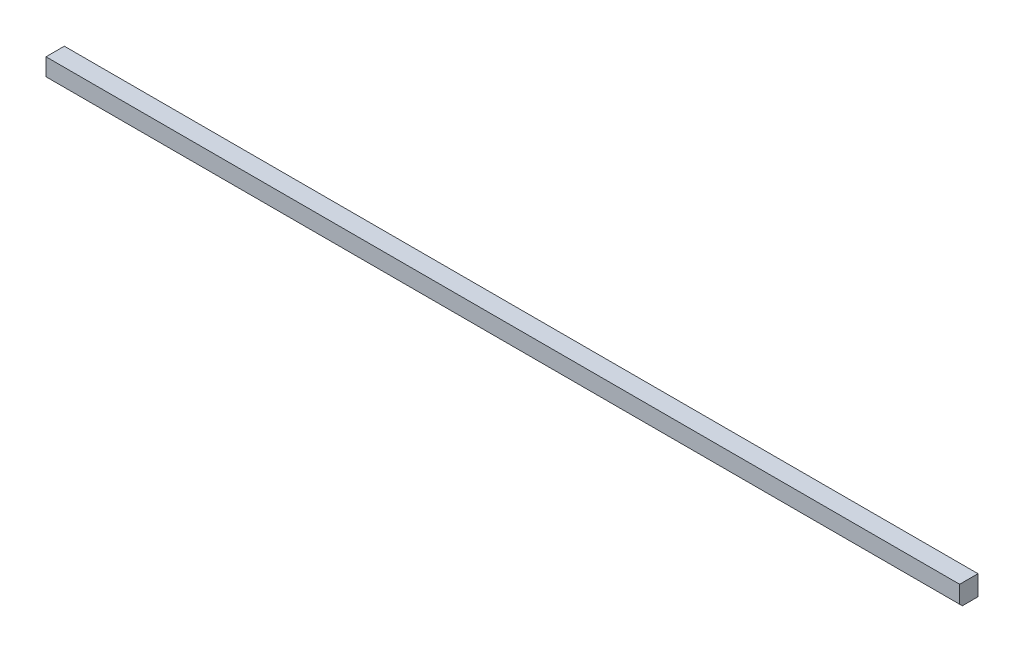
SolidWorks part; units mm, degrees
material "Oak"
ref_plane "Front Plane" through (0, 0, 0) normal (0, 0, 1) x (1, 0, 0)
ref_plane "Top Plane" through (0, 0, 0) normal (0, 1, 0) x (1, 0, 0)
ref_plane "Right Plane" through (0, 0, 0) normal (1, 0, 0) x (0, 0, -1)
sketch "Sketch1" plane through (0, 0, 0) normal (0, 1, 0) x (1, 0, 0)
  line L1 (0, 0) -> (869.95, 0)
  line L2 (0, 0) -> (0, 17.4625)
  line L3 (0, 17.4625) -> (869.95, 17.4625)
  line L4 (869.95, 0) -> (869.95, 17.4625)
  dimension "D1" = 17.4625
  dimension "D2" = 869.95
extrude "Boss-Extrude1" add sketch "Sketch1" along normal blind 19.05
chamfer "Chamfer1" distance 2.54 angle 45 1 edges at (434.975, 0, 0)
